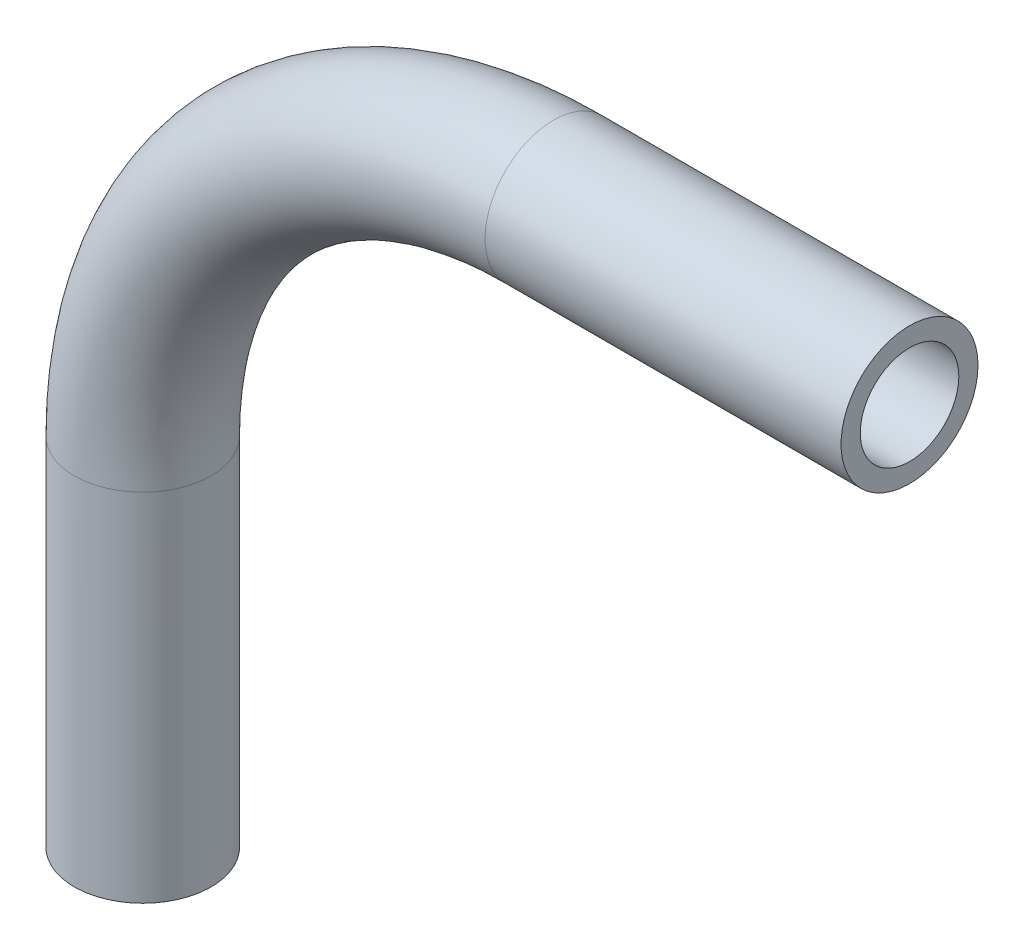
SolidWorks part; units mm, degrees
material "AISI 316 Stainless Steel Sheet (SS)"
ref_plane "Front Plane" through (0, 0, 0) normal (0, 0, 1) x (1, 0, 0)
ref_plane "Top Plane" through (0, 0, 0) normal (0, 1, 0) x (1, 0, 0)
ref_plane "Right Plane" through (0, 0, 0) normal (1, 0, 0) x (0, 0, -1)
sketch "Sketch1" plane through (0, 0, 0) normal (0, 0, 1) x (1, 0, 0)
  line L0 (0, -18.0323) -> (0, -1.5223)
  line L1 (19.05, 17.5277) -> (35.56, 17.5277)
  arc A0 (0, -1.5223) -> (19.05, 17.5277) centre (19.05, -1.5223) cw
  point P6 (0, 17.5277)
  dimension "D3" = 19.05
  dimension "D1" = 35.56
  dimension "D2" = 35.56
ref_plane "Plane1" through (35.56, 17.5277, 0) normal (1, 0, 0) x (0, 0, -1)
sketch "Sketch2" plane through (35.56, 17.5277, 0) normal (1, 0, 0) x (0, 0, -1)
  circle A0 centre (0, 0) radius 3.175
  circle A1 centre (0, 0) radius 2.286
  dimension "D1" = 6.35
  dimension "D2" = 4.572
sweep "Sweep1" add profiles "Sketch2" path "Sketch1"
